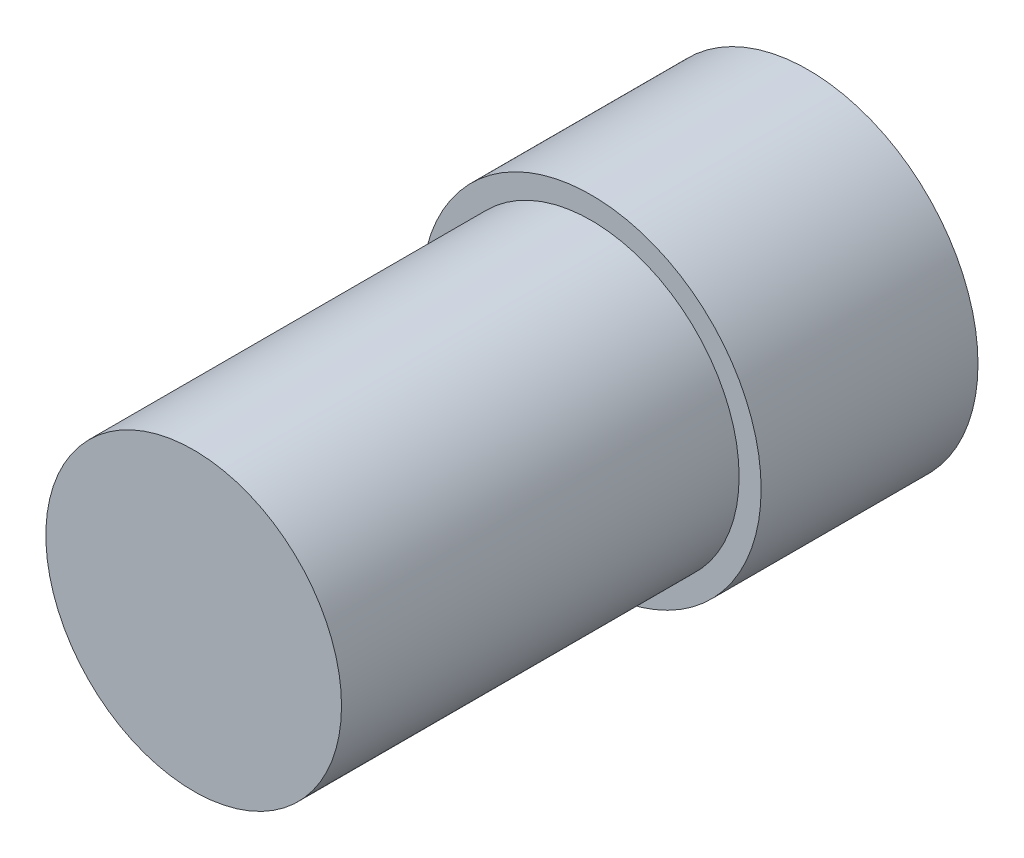
SolidWorks part; units mm, degrees
ref_plane "Front Plane" through (0, 0, 0) normal (0, 0, 1) x (1, 0, 0)
ref_plane "Top Plane" through (0, 0, 0) normal (0, 1, 0) x (1, 0, 0)
ref_plane "Right Plane" through (0, 0, 0) normal (1, 0, 0) x (0, 0, -1)
sketch "Sketch1" plane through (0, 0, 0) normal (0, 0, 1) x (1, 0, 0)
  circle A0 centre (0, 0) radius 4.699
  dimension "D1" = 9.398
extrude "Boss-Extrude1" add sketch "Sketch1" along normal blind 6
sketch "Sketch3" plane through (0, 0, 6) normal (0, 0, 1) x (1, 0, 0)
  circle A0 centre (0, 0) radius 4.09
  dimension "18" = 8.18
extrude "Boss-Extrude2" add sketch "Sketch3" along normal blind 11
